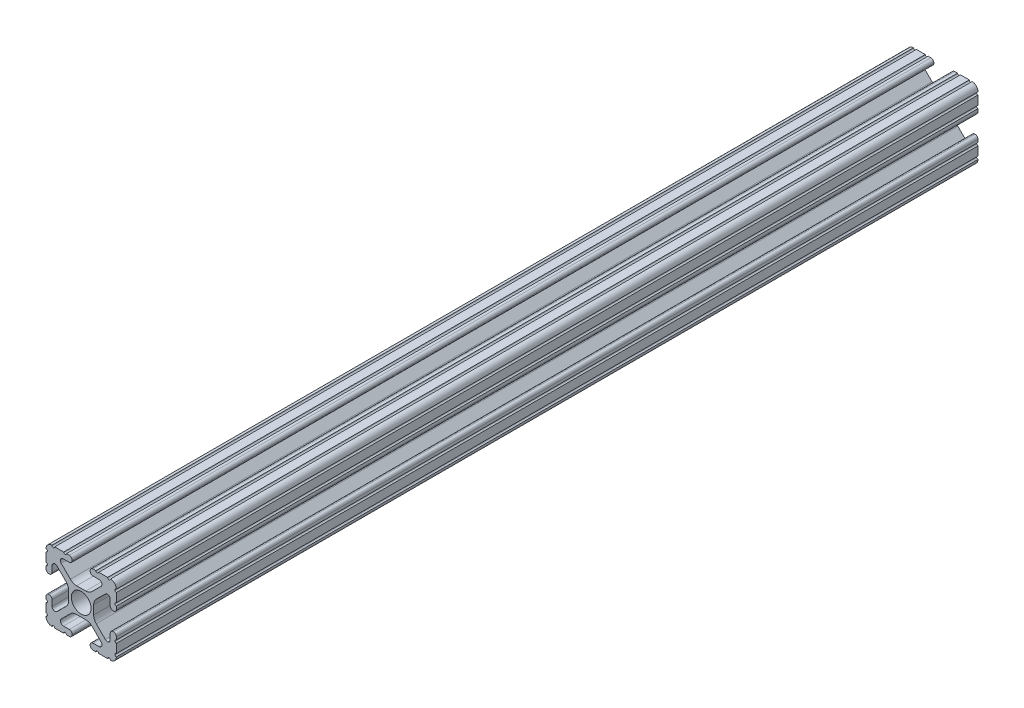
SolidWorks part; units mm, degrees
ref_plane "Front Plane" through (0, 0, 0) normal (0, 0, 1) x (1, 0, 0)
ref_plane "Top Plane" through (0, 0, 0) normal (0, 1, 0) x (1, 0, 0)
ref_plane "Right Plane" through (0, 0, 0) normal (1, 0, 0) x (0, 0, -1)
sketch "Sketch1" plane through (0, 0, 0) normal (0, 0, 1) x (1, 0, 0)
  line L88 (-7.1797, -8.6452) -> (-3.9523, -5.4237)
  line L89 (-1.7093, -4.4958) -> (1.7093, -4.4958)
  line L90 (3.9523, -5.4237) -> (7.1797, -8.6452)
  line L91 (6.4164, -10.4902) -> (4.2875, -10.4902)
  line L92 (3.2385, -11.5392) -> (3.2385, -11.651)
  line L93 (4.2875, -12.7) -> (5.3171, -12.7)
  line L94 (6.3331, -12.7) -> (9.5504, -12.7)
  line L95 (12.7, -9.5504) -> (12.7, -6.3331)
  line L96 (12.7, -5.3171) -> (12.7, -4.2875)
  line L97 (11.651, -3.2385) -> (11.5392, -3.2385)
  line L98 (10.4902, -4.2875) -> (10.4902, -6.4021)
  line L99 (8.7371, -7.1294) -> (5.441, -3.8408)
  line L100 (4.5085, -1.5932) -> (4.5085, 1.5932)
  line L101 (5.441, 3.8408) -> (8.7371, 7.1294)
  line L102 (10.4902, 6.4021) -> (10.4902, 4.2875)
  line L103 (11.5392, 3.2385) -> (11.651, 3.2385)
  line L104 (12.7, 4.2875) -> (12.7, 5.3171)
  line L105 (12.7, 6.3331) -> (12.7, 9.5504)
  line L106 (9.5504, 12.7) -> (6.3331, 12.7)
  line L107 (5.3171, 12.7) -> (4.2875, 12.7)
  line L108 (3.2385, 11.651) -> (3.2385, 11.5392)
  line L109 (4.2875, 10.4902) -> (6.4768, 10.4902)
  line L110 (7.207, 8.7244) -> (3.8983, 5.4232)
  line L111 (1.6558, 4.4958) -> (-1.6558, 4.4958)
  line L112 (-3.8983, 5.4232) -> (-7.207, 8.7244)
  line L113 (-6.4768, 10.4902) -> (-4.2875, 10.4902)
  line L114 (-3.2385, 11.5392) -> (-3.2385, 11.651)
  line L115 (-4.2875, 12.7) -> (-5.3171, 12.7)
  line L116 (-6.3331, 12.7) -> (-9.5504, 12.7)
  line L117 (-12.7, 9.5504) -> (-12.7, 6.3331)
  line L118 (-12.7, 5.3171) -> (-12.7, 4.2875)
  line L119 (-11.651, 3.2385) -> (-11.5392, 3.2385)
  line L120 (-10.4902, 4.2875) -> (-10.4902, 6.4021)
  line L121 (-8.7371, 7.1294) -> (-5.441, 3.8408)
  line L122 (-4.5085, 1.5932) -> (-4.5085, -1.5932)
  line L123 (-5.441, -3.8408) -> (-8.7371, -7.1294)
  line L124 (-10.4902, -6.4021) -> (-10.4902, -4.2875)
  line L125 (-11.5392, -3.2385) -> (-11.651, -3.2385)
  line L126 (-12.7, -4.2875) -> (-12.7, -5.3171)
  line L127 (-12.7, -6.3331) -> (-12.7, -9.5504)
  line L128 (-9.5504, -12.7) -> (-6.3331, -12.7)
  line L129 (-5.3171, -12.7) -> (-4.2875, -12.7)
  line L130 (-3.2385, -11.651) -> (-3.2385, -11.5392)
  line L131 (-4.2875, -10.4902) -> (-6.4164, -10.4902)
  circle A0 centre (0, 0) radius 3.556
  arc A104 (-7.1797, -8.6452) -> (-6.4164, -10.4902) centre (-6.4164, -9.4098) ccw
  arc A105 (-1.7093, -4.4958) -> (-3.9523, -5.4237) centre (-1.7093, -7.6708) ccw
  arc A106 (3.9523, -5.4237) -> (1.7093, -4.4958) centre (1.7093, -7.6708) ccw
  arc A107 (6.4164, -10.4902) -> (7.1797, -8.6452) centre (6.4164, -9.4098) ccw
  arc A108 (4.2875, -10.4902) -> (3.2385, -11.5392) centre (4.2875, -11.5392) ccw
  arc A109 (3.2385, -11.651) -> (4.2875, -12.7) centre (4.2875, -11.651) ccw
  arc A110 (6.3331, -12.7) -> (5.3171, -12.7) centre (5.8251, -12.7) ccw
  arc A111 (10.5664, -12.6998) -> (9.5504, -12.7) centre (10.0584, -12.7) ccw
  arc A112 (10.5664, -12.6998) -> (12.6998, -10.5664) centre (10.5918, -10.5918) ccw
  arc A113 (12.7, -9.5504) -> (12.6998, -10.5664) centre (12.7, -10.0584) ccw
  arc A114 (12.7, -5.3171) -> (12.7, -6.3331) centre (12.7, -5.8251) ccw
  arc A115 (12.7, -4.2875) -> (11.651, -3.2385) centre (11.651, -4.2875) ccw
  arc A116 (11.5392, -3.2385) -> (10.4902, -4.2875) centre (11.5392, -4.2875) ccw
  arc A117 (8.7371, -7.1294) -> (10.4902, -6.4021) centre (9.4628, -6.4021) ccw
  arc A118 (4.5085, -1.5932) -> (5.441, -3.8408) centre (7.6835, -1.5932) ccw
  arc A119 (5.441, 3.8408) -> (4.5085, 1.5932) centre (7.6835, 1.5932) ccw
  arc A120 (10.4902, 6.4021) -> (8.7371, 7.1294) centre (9.4628, 6.4021) ccw
  arc A121 (10.4902, 4.2875) -> (11.5392, 3.2385) centre (11.5392, 4.2875) ccw
  arc A122 (11.651, 3.2385) -> (12.7, 4.2875) centre (11.651, 4.2875) ccw
  arc A123 (12.7, 6.3331) -> (12.7, 5.3171) centre (12.7, 5.8251) ccw
  arc A124 (12.6998, 10.5664) -> (12.7, 9.5504) centre (12.7, 10.0584) ccw
  arc A125 (12.6998, 10.5664) -> (10.5664, 12.6998) centre (10.5918, 10.5918) ccw
  arc A126 (9.5504, 12.7) -> (10.5664, 12.6998) centre (10.0584, 12.7) ccw
  arc A127 (5.3171, 12.7) -> (6.3331, 12.7) centre (5.8251, 12.7) ccw
  arc A128 (4.2875, 12.7) -> (3.2385, 11.651) centre (4.2875, 11.651) ccw
  arc A129 (3.2385, 11.5392) -> (4.2875, 10.4902) centre (4.2875, 11.5392) ccw
  arc A130 (7.207, 8.7244) -> (6.4768, 10.4902) centre (6.4768, 9.4563) ccw
  arc A131 (1.6558, 4.4958) -> (3.8983, 5.4232) centre (1.6558, 7.6708) ccw
  arc A132 (-3.8983, 5.4232) -> (-1.6558, 4.4958) centre (-1.6558, 7.6708) ccw
  arc A133 (-6.4768, 10.4902) -> (-7.207, 8.7244) centre (-6.4768, 9.4563) ccw
  arc A134 (-4.2875, 10.4902) -> (-3.2385, 11.5392) centre (-4.2875, 11.5392) ccw
  arc A135 (-3.2385, 11.651) -> (-4.2875, 12.7) centre (-4.2875, 11.651) ccw
  arc A136 (-6.3331, 12.7) -> (-5.3171, 12.7) centre (-5.8251, 12.7) ccw
  arc A137 (-10.5664, 12.6998) -> (-9.5504, 12.7) centre (-10.0584, 12.7) ccw
  arc A138 (-10.5664, 12.6998) -> (-12.6998, 10.5664) centre (-10.5918, 10.5918) ccw
  arc A139 (-12.7, 9.5504) -> (-12.6998, 10.5664) centre (-12.7, 10.0584) ccw
  arc A140 (-12.7, 5.3171) -> (-12.7, 6.3331) centre (-12.7, 5.8251) ccw
  arc A141 (-12.7, 4.2875) -> (-11.651, 3.2385) centre (-11.651, 4.2875) ccw
  arc A142 (-11.5392, 3.2385) -> (-10.4902, 4.2875) centre (-11.5392, 4.2875) ccw
  arc A143 (-8.7371, 7.1294) -> (-10.4902, 6.4021) centre (-9.4628, 6.4021) ccw
  arc A144 (-4.5085, 1.5932) -> (-5.441, 3.8408) centre (-7.6835, 1.5932) ccw
  arc A145 (-5.441, -3.8408) -> (-4.5085, -1.5932) centre (-7.6835, -1.5932) ccw
  arc A146 (-10.4902, -6.4021) -> (-8.7371, -7.1294) centre (-9.4628, -6.4021) ccw
  arc A147 (-10.4902, -4.2875) -> (-11.5392, -3.2385) centre (-11.5392, -4.2875) ccw
  arc A148 (-11.651, -3.2385) -> (-12.7, -4.2875) centre (-11.651, -4.2875) ccw
  arc A149 (-12.7, -6.3331) -> (-12.7, -5.3171) centre (-12.7, -5.8251) ccw
  arc A150 (-12.6998, -10.5664) -> (-12.7, -9.5504) centre (-12.7, -10.0584) ccw
  arc A151 (-12.6998, -10.5664) -> (-10.5664, -12.6998) centre (-10.5918, -10.5918) ccw
  arc A152 (-9.5504, -12.7) -> (-10.5664, -12.6998) centre (-10.0584, -12.7) ccw
  arc A153 (-5.3171, -12.7) -> (-6.3331, -12.7) centre (-5.8251, -12.7) ccw
  arc A154 (-4.2875, -12.7) -> (-3.2385, -11.651) centre (-4.2875, -11.651) ccw
  arc A155 (-3.2385, -11.5392) -> (-4.2875, -10.4902) centre (-4.2875, -11.5392) ccw
  dimension "D1" = 7.112
extrude "Boss-Extrude1" add sketch "Sketch1" along normal mid plane 311.15
